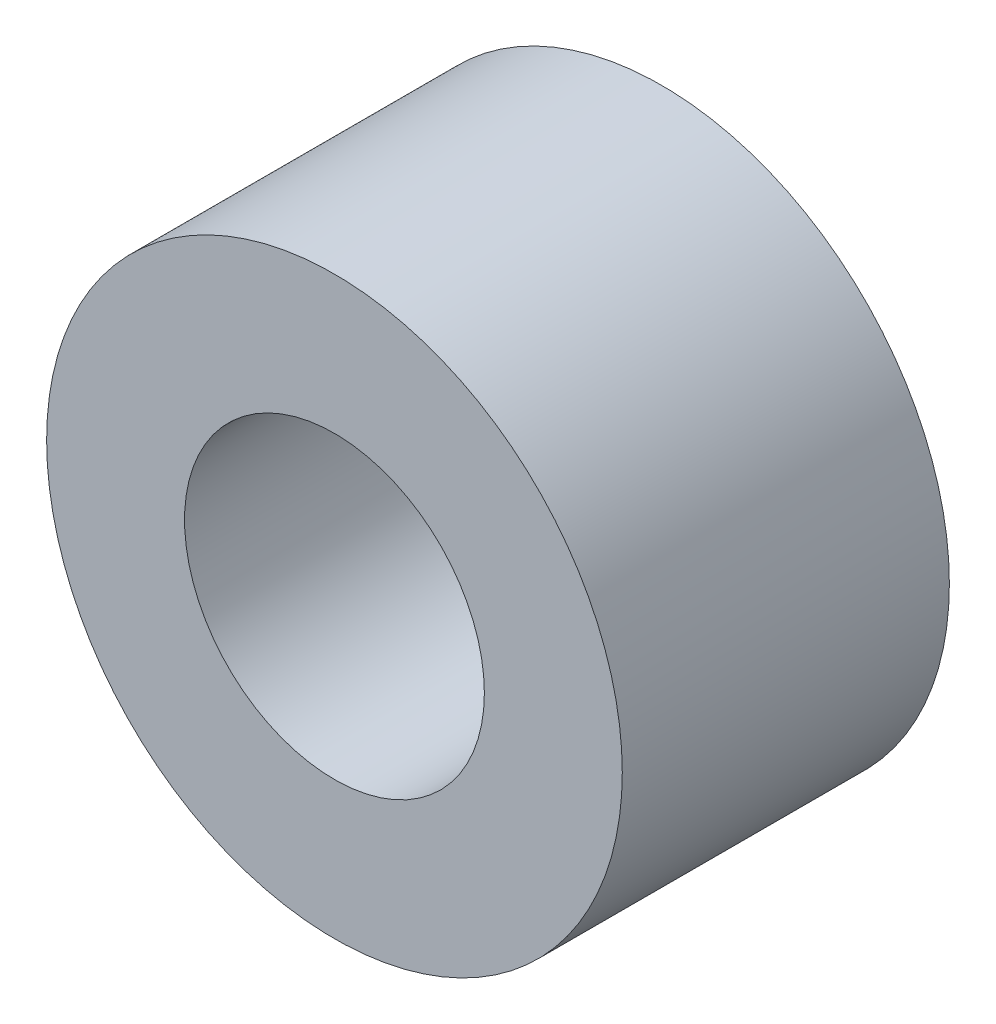
SolidWorks part; units mm, degrees
ref_plane "Front Plane" through (0, 0, 0) normal (0, 0, 1) x (1, 0, 0)
ref_plane "Top Plane" through (0, 0, 0) normal (0, 1, 0) x (1, 0, 0)
ref_plane "Right Plane" through (0, 0, 0) normal (1, 0, 0) x (0, 0, -1)
sketch "Sketch1" plane through (0, 0, 0) normal (0, 0, 1) x (1, 0, 0)
  circle A0 centre (0, 0) radius 4.3656
  circle A1 centre (0, 0) radius 8.382
  dimension "D1" = 8.7312
  dimension "D2" = 16.764
extrude "Boss-Extrude1" add sketch "Sketch1" along normal blind 9.525
